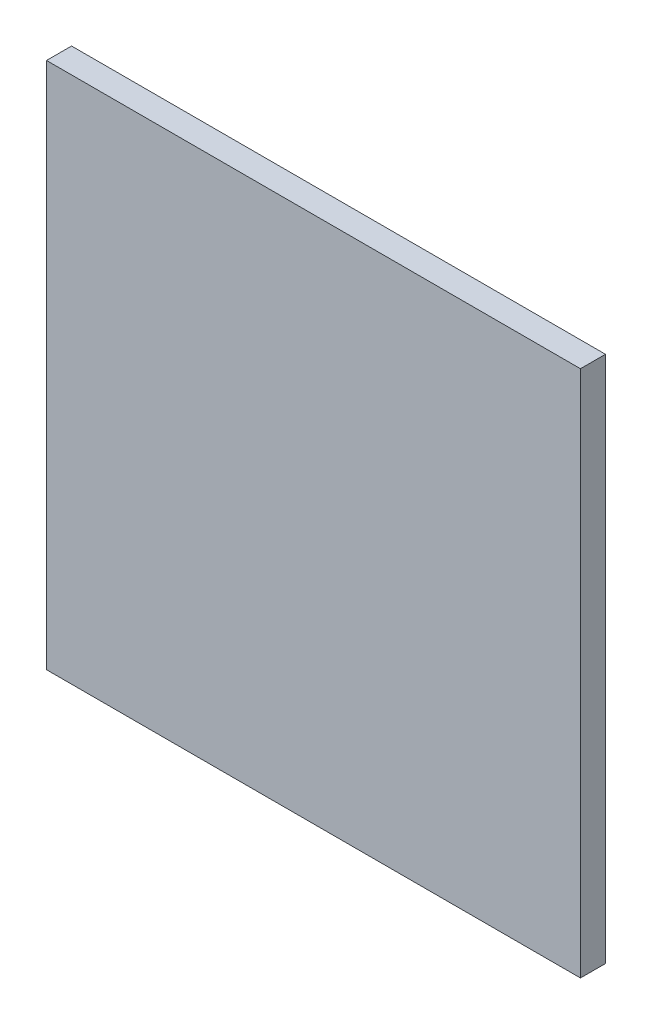
SolidWorks part; units mm, degrees
material "Perspex (TM) GS Acrylic Cast Sheet"
ref_plane "Front Plane" through (0, 0, 0) normal (0, 0, 1) x (1, 0, 0)
ref_plane "Top Plane" through (0, 0, 0) normal (0, 1, 0) x (1, 0, 0)
ref_plane "Right Plane" through (0, 0, 0) normal (1, 0, 0) x (0, 0, -1)
sketch "Sketch1" plane through (0, 0, 0) normal (0, 0, 1) x (1, 0, 0)
  line L1 (-32, -31.625) -> (32, -31.625)
  line L2 (-32, -31.625) -> (-32, 31.625)
  line L3 (-32, 31.625) -> (32, 31.625)
  line L4 (32, -31.625) -> (32, 31.625)
  line L5 (-32, -31.625) -> (32, 31.625) construction
  line L6 (-32, 31.625) -> (32, -31.625) construction
  point P0 (0, 0)
  dimension "D1" = 64
  dimension "D2" = 63.25
extrude "Boss-Extrude1" add sketch "Sketch1" along normal blind 3
